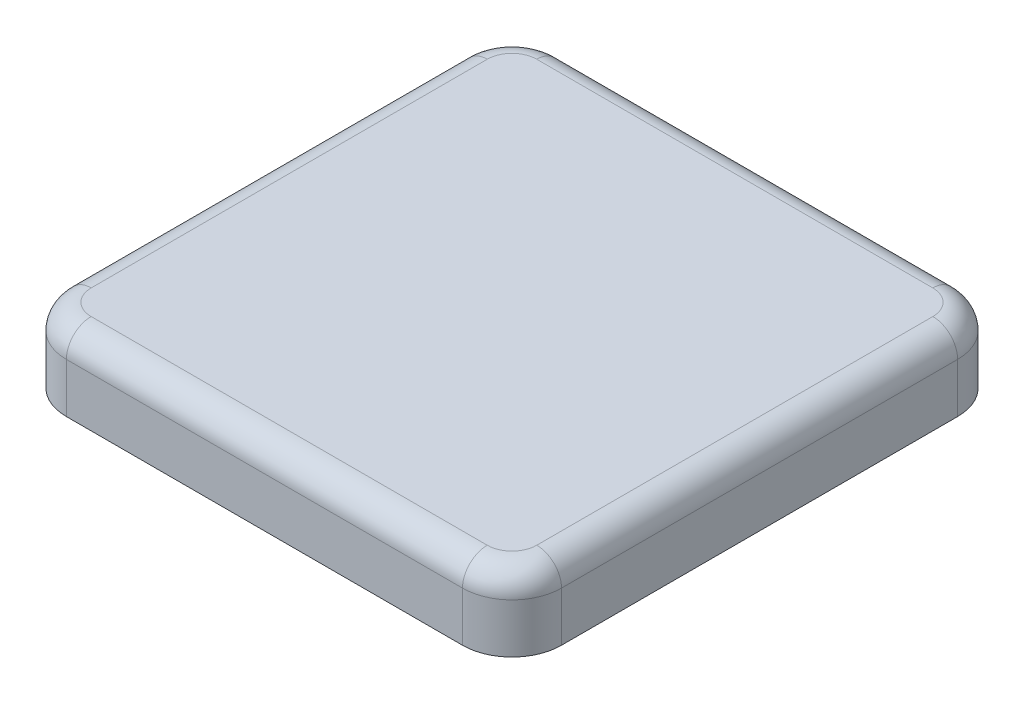
SolidWorks part; units mm, degrees
ref_plane "정면" through (0, 0, 0) normal (0, 0, 1) x (1, 0, 0)
ref_plane "윗면" through (0, 0, 0) normal (0, 1, 0) x (1, 0, 0)
ref_plane "우측면" through (0, 0, 0) normal (1, 0, 0) x (0, 0, -1)
sketch "스케치1" plane through (0, 0, 0) normal (0, 1, 0) x (1, 0, 0)
  line L1 (-2.5, 2.5) -> (2.5, 2.5)
  line L2 (-2.5, 2.5) -> (-2.5, -2.5)
  line L3 (-2.5, -2.5) -> (2.5, -2.5)
  line L4 (2.5, 2.5) -> (2.5, -2.5)
  line L5 (-2.5, 2.5) -> (2.5, -2.5) construction
  line L6 (-2.5, -2.5) -> (2.5, 2.5) construction
  point P0 (0, 0)
  dimension "D1" = 5
  dimension "D2" = 5
extrude "보스-돌출1" add sketch "스케치1" along normal blind 2.5
sketch "스케치2" plane through (0, 2.5, 0) normal (0, 1, 0) x (1, 0, 0)
  line L0 (-2.5, 2.5) -> (2.5, 2.5) construction
  line L2 (-2, -2) -> (2, -2)
  line L3 (-2, -2) -> (-2, 2)
  line L4 (-2, 2) -> (2, 2)
  line L5 (2, -2) -> (2, 2)
  line L6 (-2, -2) -> (2, 2) construction
  line L7 (-2, 2) -> (2, -2) construction
  point P4 (0, 0)
  dimension "D1" = 4
  dimension "D2" = 4
extrude "컷-돌출1" cut sketch "스케치2" against normal blind 2.5
sketch "스케치4" plane through (0, 2.5, 0) normal (0, 1, 0) x (1, 0, 0)
  line L1 (-2.5, -2.5) -> (2.5, -2.5)
  line L2 (-2.5, -2.5) -> (-2.5, 2.5)
  line L3 (-2.5, 2.5) -> (2.5, 2.5)
  line L4 (2.5, -2.5) -> (2.5, 2.5)
  line L5 (-2.5, -2.5) -> (2.5, 2.5) construction
  line L6 (-2.5, 2.5) -> (2.5, -2.5) construction
  point P0 (0, 0)
extrude "보스-돌출3" add sketch "스케치4" along normal blind 2
sketch "스케치5" plane through (0, 4.5, 0) normal (0, 1, 0) x (1, 0, 0)
  line L1 (-10, -10) -> (10, -10)
  line L2 (-10, -10) -> (-10, 10)
  line L3 (-10, 10) -> (10, 10)
  line L4 (10, -10) -> (10, 10)
  line L5 (-10, -10) -> (10, 10) construction
  line L6 (-10, 10) -> (10, -10) construction
  point P0 (0, 0)
  dimension "D1" = 20
  dimension "D2" = 20
extrude "보스-돌출4" add sketch "스케치5" along normal blind 3
fillet "필렛6" radius 2 4 edges at (-10, 6, -10) (10, 6, -10) (10, 6, 10) (-10, 6, 10)
fillet "필렛7" radius 1 8 edges at (0, 7.5, 10) (-9.4142, 7.5, 9.4142) (-10, 7.5, 0) (-9.4142, 7.5, -9.4142) (0, 7.5, -10) (9.4142, 7.5, -9.4142) (9.4142, 7.5, 9.4142) (10, 7.5, 0)
